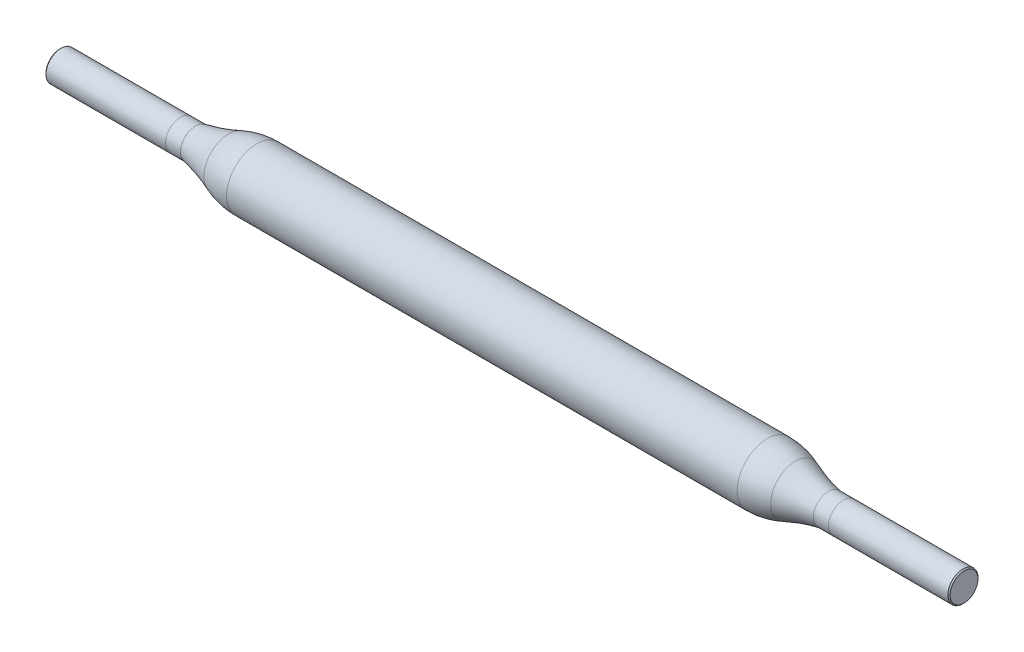
SolidWorks part; units mm, degrees
ref_plane "Front Plane" through (0, 0, 0) normal (0, 0, 1) x (1, 0, 0)
ref_plane "Top Plane" through (0, 0, 0) normal (0, 1, 0) x (1, 0, 0)
ref_plane "Right Plane" through (0, 0, 0) normal (1, 0, 0) x (0, 0, -1)
sketch "Sketch2" plane through (0, 0, 0) normal (0, 0, 1) x (1, 0, 0)
  line L0 (-30, 0) -> (30, 0)
  line L1 (-30, 0) -> (-30, 1)
  line L2 (30, 0) -> (30, 1)
  line L3 (-30, 1) -> (-21, 1)
  line L4 (30, 1) -> (21, 1)
  line L5 (-16.9405, 2) -> (16.9405, 2)
  arc A0 (-21, 1) -> (-18.8074, 1.6384) centre (-23.1066, 12.3199) ccw
  arc A1 (21, 1) -> (18.8074, 1.6384) centre (23.1066, 12.3199) cw
  arc A2 (16.9405, 2) -> (18.8074, 1.6384) centre (16.9405, -3) cw
  arc A3 (-16.9405, 2) -> (-18.8074, 1.6384) centre (-16.9405, -3) ccw
  point P2 (0, 0)
  point P10 (0, 2)
  point P13 (0, 0)
  point P16 (18, 2)
  dimension "D5" = 3
  dimension "D6" = 11.5143
  dimension "D7" = 5
  dimension "D1" = 60
  dimension "D2" = 1
  dimension "D3" = 9
  dimension "D4" = 2
revolve "Revolve1" add sketch "Sketch2" angle 360 about L0
sketch "Sketch3" plane through (0, 0, 0) normal (0, 0, 1) x (1, 0, 0)
  line L0 (-22, 4.9043) -> (-22, -7.0651)
  line L1 (22, 5.3492) -> (22, -7.0715)
  line L2 (-30, 1) -> (-30, -1) construction
  line L3 (30, -1) -> (30, 1) construction
  dimension "D1" = 8
  dimension "D2" = 8
split line "Split Line1"
chamfer "Chamfer1" distance 0.075 angle 45 2 edges at (-30, -1, 0) (30, -1, 0)
